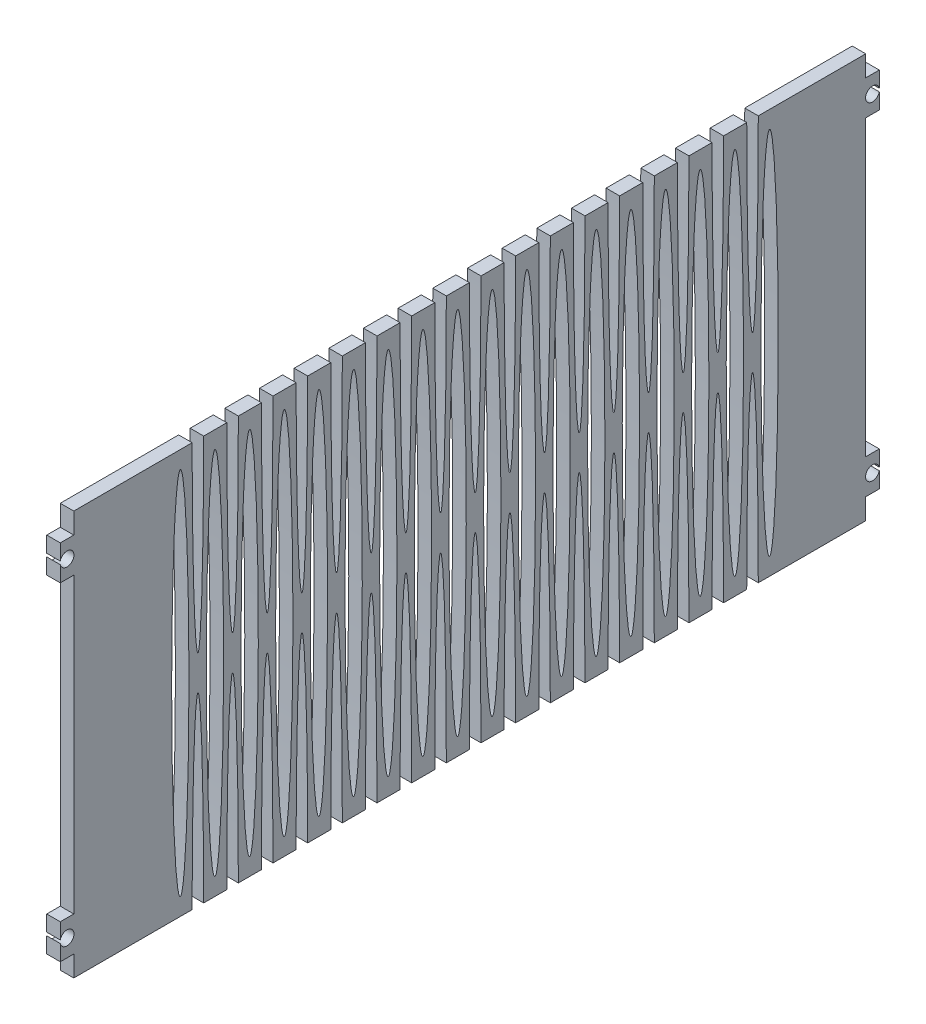
SolidWorks part; units mm, degrees
ref_plane "Front Plane" through (0, 0, 0) normal (0, 0, 1) x (1, 0, 0)
ref_plane "Top Plane" through (0, 0, 0) normal (0, 1, 0) x (1, 0, 0)
ref_plane "Right Plane" through (0, 0, 0) normal (1, 0, 0) x (0, 0, -1)
sketch "Sketch2" plane through (0, 0, 0) normal (1, 0, 0) x (0, 0, -1)
  line L1 (0, 44.45) -> (198.12, 44.45)
  line L2 (0, 44.45) -> (0, -44.45)
  line L3 (0, -44.45) -> (198.12, -44.45)
  line L4 (198.12, 44.45) -> (198.12, -44.45)
  dimension "D1" = 198.12
  dimension "D2" = 88.9
extrude "Boss-Extrude1" add sketch "Sketch2" along normal blind 2.9718
sketch "Sketch3" plane through (2.9718, 0, 0) normal (1, 0, 0) x (0, 0, -1)
  ellipse E0 centre (47.434, 0) end of major axis (47.434, 40.64) minor radius 1.905
  dimension "D1" = 3.81
  dimension "D2" = 81.28
extrude "Cut-Extrude1" cut sketch "Sketch3" against normal through all
pattern_linear "LPattern1" count 18 spacing 7.62 along (0, 0, 1) of "Cut-Extrude1"
sketch "Sketch4" plane through (2.9718, 0, 0) normal (1, 0, 0) x (0, 0, -1)
  line L0 (0, -44.45) -> (198.12, -44.45) construction
  line L1 (0, 44.45) -> (0, -44.45) construction
  line L2 (50.038, -44.45) -> (52.578, -44.45)
  ellipse E0 centre (51.308, -44.45) end of major axis (51.308, -3.81) minor radius 1.27 (52.578, -44.45) -> (50.038, -44.45) ccw
  dimension "D1" = 81.28
  dimension "D2" = 2.54
  dimension "D3" = 51.308
extrude "Cut-Extrude2" cut sketch "Sketch4" against normal through all
pattern_linear "LPattern2" count 17 spacing 7.62 along (0, 0, 1) of "Cut-Extrude2"
mirror "Mirror1" about plane through (0, 0, 0) normal (0, 1, 0) of "LPattern2", "Cut-Extrude2"
sketch "Sketch5" plane through (2.9718, 0, 0) normal (1, 0, 0) x (0, 0, -1)
  line L3 (-24.6799, 59.4245) -> (24.0148, 59.4245)
  line L4 (-24.6799, 59.4245) -> (-24.6799, -57.0216)
  line L5 (-24.6799, -57.0216) -> (24.0148, -57.0216)
  line L6 (24.0148, 59.4245) -> (24.0148, -57.0216)
extrude "Cut-Extrude3" cut sketch "Sketch5" against normal through all
sketch "Sketch7" plane through (0, 0, 0) normal (1, 0, 0) x (0, 0, -1)
  line L0 (24.0148, -44.45) -> (24.0148, 44.45) construction
  line L1 (21.043, 39.878) -> (24.0148, 39.878)
  line L2 (21.043, 39.878) -> (21.043, 32.258)
  line L3 (21.043, 32.258) -> (24.0148, 32.258)
  line L4 (24.0148, 39.878) -> (24.0148, 32.258)
  line L5 (50.038, 44.45) -> (24.0148, 44.45) construction
  line L6 (24.0148, 0) -> (198.12, 0) construction
  line L7 (198.12, -44.45) -> (198.12, 44.45) construction
  line L8 (111.0674, 0) -> (111.0674, 62.3627) construction
  line L9 (201.0918, 32.258) -> (198.12, 32.258)
  line L10 (198.12, 39.878) -> (198.12, 32.258)
  line L11 (201.0918, 39.878) -> (201.0918, 32.258)
  line L12 (201.0918, 39.878) -> (198.12, 39.878)
  line L13 (201.0918, -32.258) -> (198.12, -32.258)
  line L14 (201.0918, -39.878) -> (201.0918, -32.258)
  line L15 (201.0918, -39.878) -> (198.12, -39.878)
  line L16 (198.12, -39.878) -> (198.12, -32.258)
  line L17 (21.043, -32.258) -> (24.0148, -32.258)
  line L18 (24.0148, -39.878) -> (24.0148, -32.258)
  line L19 (21.043, -39.878) -> (24.0148, -39.878)
  line L20 (21.043, -39.878) -> (21.043, -32.258)
  dimension "D1" = 7.62
  dimension "D2" = 2.9718
  dimension "D3" = 4.572
extrude "Boss-Extrude2" add sketch "Sketch7" along normal blind 2.9718
sketch "Sketch8" plane through (2.9718, 0, 0) normal (1, 0, 0) x (0, 0, -1)
  line L0 (24.0148, 39.878) -> (21.043, 39.878) construction
  line L1 (24.0148, 39.878) -> (24.0148, 44.45) construction
  line L2 (24.0148, 0) -> (198.12, 0) construction
  line L3 (24.0148, -32.258) -> (24.0148, 32.258) construction
  line L4 (198.12, -32.258) -> (198.12, 32.258) construction
  line L5 (111.0674, 0) -> (111.0674, 54.8961) construction
  circle A0 centre (22.5289, 36.068) radius 1.524
  circle A1 centre (199.6059, 36.068) radius 1.524
  circle A2 centre (199.6059, -36.068) radius 1.524
  circle A3 centre (22.5289, -36.068) radius 1.524
  dimension "D1" = 3.048
  dimension "D2" = 3.81
  dimension "D3" = 1.4859
extrude "Cut-Extrude4" cut sketch "Sketch8" against normal through all
